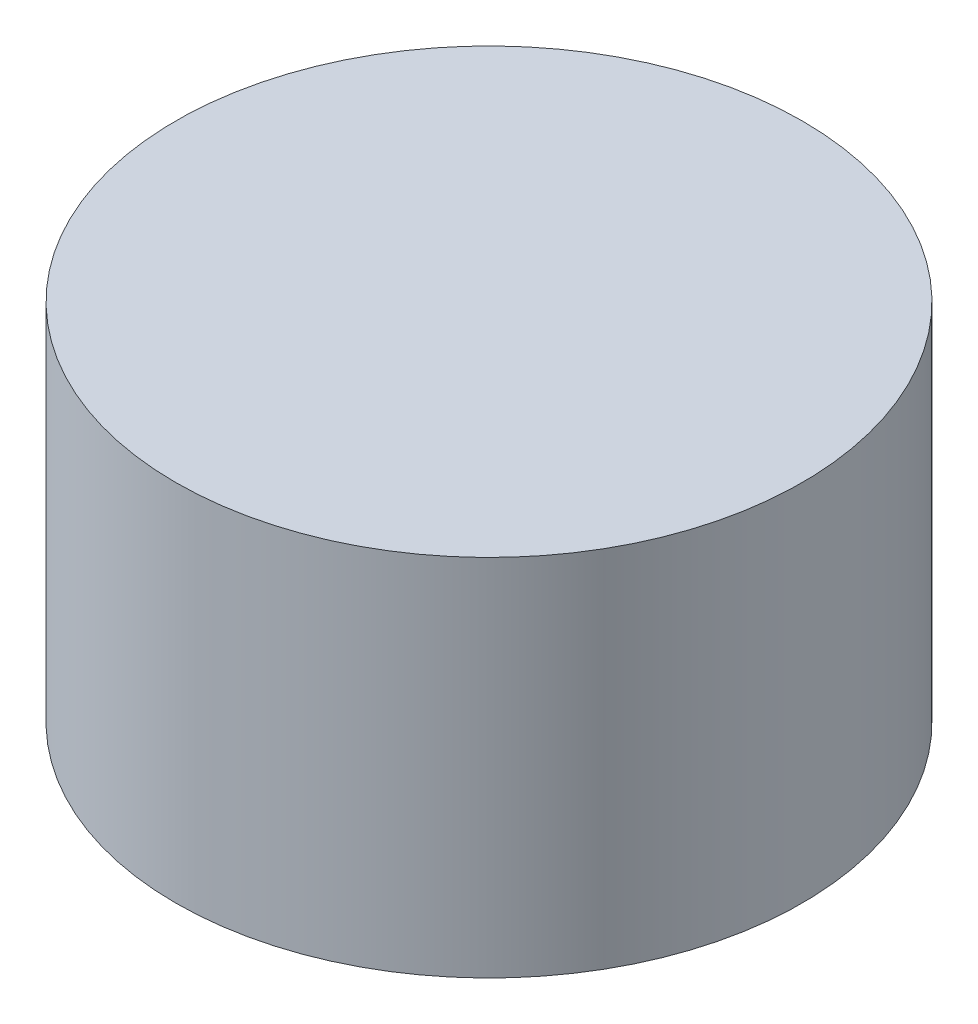
SolidWorks part; units mm, degrees
ref_plane "Front Plane" through (0, 0, 0) normal (0, 0, 1) x (1, 0, 0)
ref_plane "Top Plane" through (0, 0, 0) normal (0, 1, 0) x (1, 0, 0)
ref_plane "Right Plane" through (0, 0, 0) normal (1, 0, 0) x (0, 0, -1)
sketch "Sketch1" plane through (0, 0, 0) normal (0, 1, 0) x (1, 0, 0)
  circle A0 centre (0, 0) radius 2.15
  dimension "D1" = 4.3
extrude "Boss-Extrude1" add sketch "Sketch1" along normal blind 2.5
